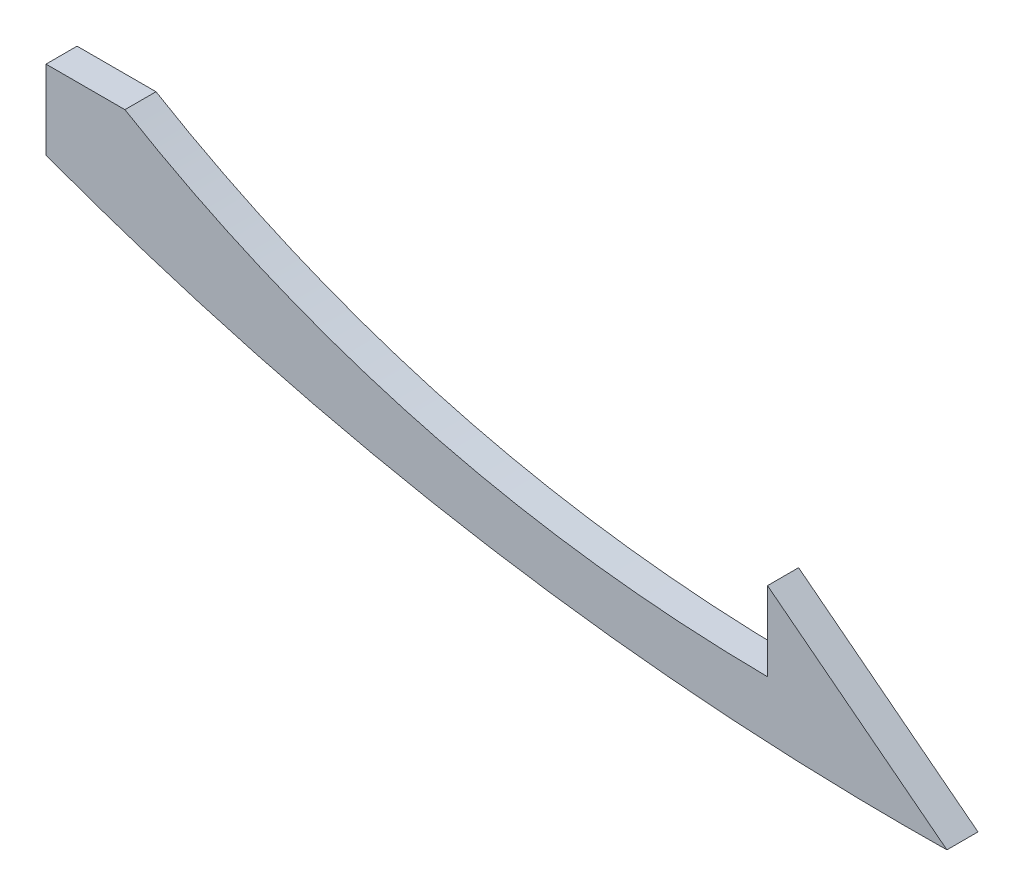
SolidWorks part; units mm, degrees
ref_plane "Front Plane" through (0, 0, 0) normal (0, 0, 1) x (1, 0, 0)
ref_plane "Top Plane" through (0, 0, 0) normal (0, 1, 0) x (1, 0, 0)
ref_plane "Right Plane" through (0, 0, 0) normal (1, 0, 0) x (0, 0, -1)
sketch "Sketch1" plane through (0, 0, 0) normal (0, 0, 1) x (1, 0, 0)
  line L0 (0, -6.35) -> (0, 6.35)
  line L1 (0, 6.35) -> (12.7, 6.35)
  line L2 (116.0939, -20.9749) -> (116.0939, -8.2749)
  line L3 (116.0939, -8.2749) -> (144.9605, -30.6605)
  line L5 (0, 12.7) -> (0, -12.7) construction
  line L6 (0, -12.7) -> (17.9605, -30.6605) construction
  line L7 (17.9605, -30.6605) -> (144.9605, -30.6605) construction
  spline S0 degree 2 poles (144.9605, -30.6605) (68.4115, -31.7178) (0, -6.35) knots 0 0 0 0.711551 0.711551 0.711551
  spline S1 degree 2 poles (116.0939, -20.9749) (57.7825, -20.4536) (12.7, 6.35) knots 0 0 0 0.666344 0.666344 0.666344
  dimension "D1" = 12.7
  dimension "D2" = 12.7
  dimension "D3" = 12.7
  dimension "D6" = 25.4
  dimension "D8" = 25.4
  dimension "D9" = 127
extrude "Boss-Extrude1" add sketch "Sketch1" along normal blind 5
